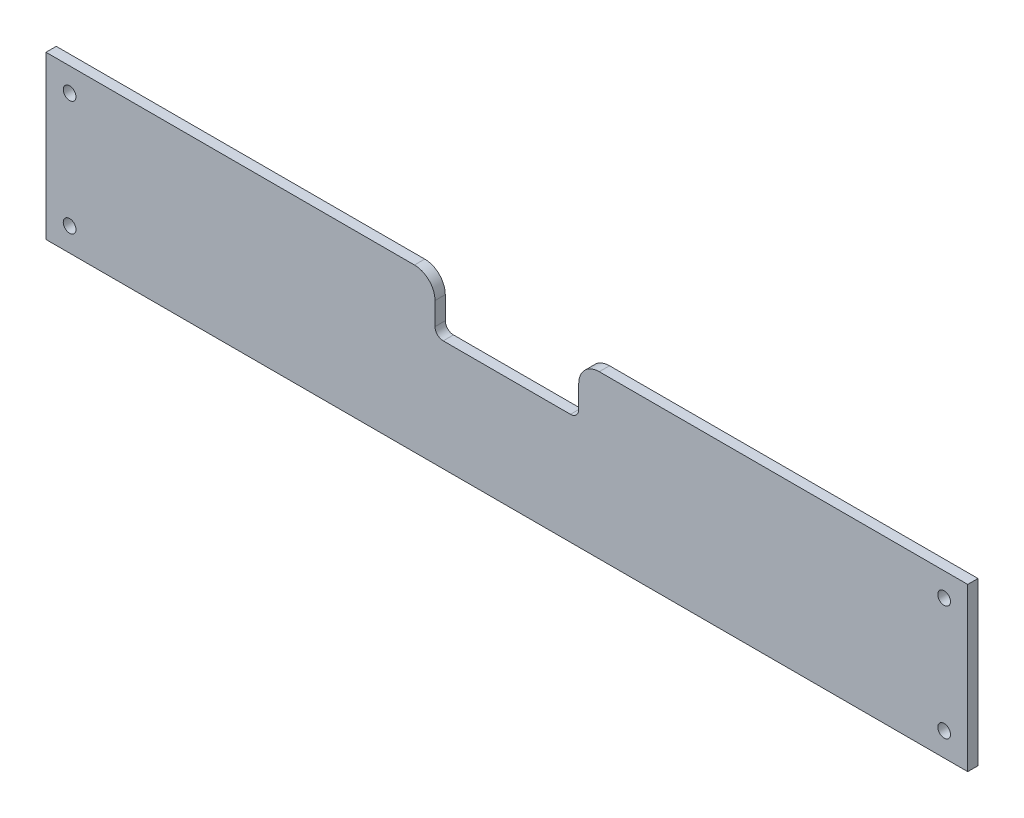
SolidWorks part; units mm, degrees
material "PMMA"
ref_plane "Piano frontale" through (0, 0, 0) normal (0, 0, 1) x (1, 0, 0)
ref_plane "Piano superiore" through (0, 0, 0) normal (0, 1, 0) x (1, 0, 0)
ref_plane "Piano destro" through (0, 0, 0) normal (1, 0, 0) x (0, 0, -1)
sketch "f" plane through (0, 0, 0) normal (0, 0, 1) x (1, 0, 0)
  line L0 (0, 0) -> (0, 79)
  line L1 (0, 79) -> (179.5, 79)
  line L2 (449, 79) -> (449, 0)
  line L3 (449, 0) -> (0, 0)
  line L4 (0, 39.5) -> (449, 39.5) construction
  line L5 (224.5, 42) -> (224.5, 123.488) construction
  line L6 (255.5, 54) -> (193.5, 54)
  line L7 (189.5, 58) -> (189.5, 69)
  line L8 (259.5, 58) -> (259.5, 69)
  line L9 (269.5, 79) -> (449, 79)
  line L10 (449, 79) -> (224.5, 0) construction
  line L11 (334, 39.5) -> (334, 81.5) construction
  line L12 (224.5, 0) -> (0, 79) construction
  line L13 (112.25, 42) -> (112.25, 84) construction
  circle A0 centre (11.5, 67.5) radius 3.1
  circle A1 centre (437.5, 67.5) radius 3.1
  circle A2 centre (11.5, 11.5) radius 3.1
  circle A3 centre (437.5, 11.5) radius 3.1
  arc A4 (189.5, 69) -> (179.5, 79) centre (179.5, 69) ccw
  arc A5 (259.5, 69) -> (269.5, 79) centre (269.5, 69) cw
  arc A6 (259.5, 58) -> (255.5, 54) centre (255.5, 58) cw
  arc A7 (189.5, 58) -> (193.5, 54) centre (193.5, 58) ccw
  point P23 (224.5, 54)
  point P27 (189.5, 79)
  point P32 (259.5, 79)
  point P35 (259.5, 54)
  point P38 (189.5, 54)
  dimension "D3" = 11.5
  dimension "D4" = 11.5
  dimension "D6" = 35
  dimension "D9" = 10
  dimension "D10" = 4
  dimension "D5" = 6.2
  dimension "D8" = 10
  dimension "D1" = 79
  dimension "D2" = 449
  dimension "D7" = 25
extrude "Estrusione-Estrusione1" add sketch "f" along normal blind 5
